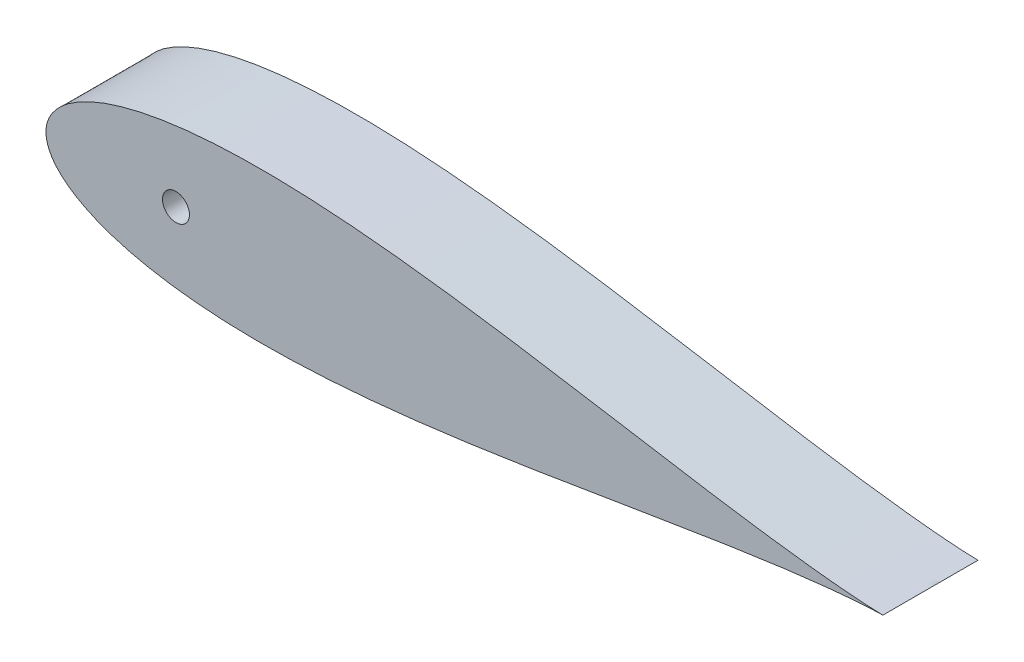
SolidWorks part; units mm, degrees
ref_plane "Front Plane" through (0, 0, 0) normal (0, 0, 1) x (1, 0, 0)
ref_plane "Top Plane" through (0, 0, 0) normal (0, 1, 0) x (1, 0, 0)
ref_plane "Right Plane" through (0, 0, 0) normal (1, 0, 0) x (0, 0, -1)
sketch "Sketch1" plane through (0, 0, 0) normal (0, 0, 1) x (1, 0, 0)
  line L0 (100, 0) -> (0, 0) construction
  line L1 (1.2169, -991.9959) -> (1.2169, 49008.0041) construction
  line L2 (93.345, 0) -> (114.935, 0) construction
  line L3 (125.634, 0) -> (131.6629, 0) construction
  line L4 (643.5991, 0) -> (643.5991, -1.016)
  line L9 (0, 0) -> (643.9668, 0)
  line L13 (460.661, 0) -> (473.361, 0)
  circle A0 centre (104.14, 0) radius 10.795 construction
  arc A1 (1.2169, -4.6585) -> (1.2169, 4.6585) centre (9.525, 0) cw
  arc A2 (641.5671, 0) -> (644.1071, 0) centre (642.8371, 0) ccw
  circle A4 centre (104.14, 0) radius 10.795
  circle A9 centre (40.64, 0) radius 12.7
  circle A14 centre (642.3793, 0) radius 1.5875 construction
  arc A15 (642.5108, -1.582) -> (642.5108, 1.582) centre (642.3793, 0) ccw
  spline S2 degree 3 poles (666.3448, -0.0547) (672.2538, 0) (666.3448, 0.0547) (662.8509, 0.2344) (656.505, 0.5436) (649.293, 1.0348) (640.4916, 1.7319) (630.4138, 2.6634) (619.0141, 3.8493) (606.375, 5.3044) (592.5439, 7.0376) (577.5855, 9.0506) (561.5643, 11.3389) (544.5497, 13.8907) (526.6141, 16.6877) (507.8326, 19.7051) (488.2827, 22.9117) (468.0444, 26.2704) (447.1994, 29.739) (425.8316, 33.2703) (404.0263, 36.8132) (381.8707, 40.3133) (359.4533, 43.7135) (336.8645, 46.9554) (314.1962, 49.9798) (291.5418, 52.7277) (268.9963, 55.1412) (246.6566, 57.1646) (224.6209, 58.7452) (202.9892, 59.8341) (181.8631, 60.3875) (161.3458, 60.367) (141.542, 59.7399) (122.5581, 58.4818) (104.5023, 56.5743) (87.485, 54.0089) (71.6197, 50.7848) (57.0237, 46.9125) (43.8205, 42.415) (32.1416, 37.3322) (22.1291, 31.7315) (13.9324, 25.7264) (7.6896, 19.5132) (3.4631, 13.4204) (1.1063, 7.9234) (0.1546, 3.5138) (-0.0622, 0) (0.1546, -3.5138) (1.1063, -7.9234) (3.4631, -13.4204) (7.6896, -19.5132) (13.9324, -25.7264) (22.1291, -31.7315) (32.1416, -37.3322) (43.8205, -42.415) (57.0237, -46.9125) (71.6197, -50.7848) (87.485, -54.0089) (104.5023, -56.5743) (122.5581, -58.4818) (141.542, -59.7399) (161.3458, -60.367) (181.8631, -60.3875) (202.9892, -59.8341) (224.6209, -58.7452) (246.6566, -57.1646) (268.9963, -55.1412) (291.5418, -52.7277) (314.1962, -49.9798) (336.8645, -46.9554) (359.4533, -43.7135) (381.8707, -40.3133) (404.0263, -36.8132) (425.8316, -33.2703) (447.1994, -29.739) (468.0444, -26.2704) (488.2827, -22.9117) (507.8326, -19.7051) (526.6141, -16.6877) (544.5497, -13.8907) (561.5643, -11.3389) (577.5855, -9.0506) (592.5439, -7.0376) (606.375, -5.3044) (619.0141, -3.8493) (630.4138, -2.6634) (640.4916, -1.7319) (649.293, -1.0348) (656.505, -0.5436) (662.8509, -0.2344) (666.3448, -0.0547) (672.2538, 0) (666.3448, 0.0547) knots -0.009667 -0.005395 -0.002168 0 0.002168 0.005395 0.009667 0.014967 0.021271 0.028553 0.036781 0.04592 0.055932 0.066773 0.078397 0.090755 0.103793 0.117456 0.131686 0.146422 0.1616 0.177156 0.193024 0.209135 0.225421 0.241812 0.258238 0.274629 0.290914 0.307025 0.322893 0.338448 0.353626 0.368361 0.38259 0.396253 0.40929 0.421647 0.43327 0.444109 0.454119 0.463255 0.471479 0.478755 0.485052 0.490344 0.49461 0.497833 0.5 0.502167 0.50539 0.509656 0.514948 0.521245 0.528521 0.536745 0.545881 0.555891 0.56673 0.578353 0.59071 0.603747 0.61741 0.631639 0.646374 0.661552 0.677107 0.692975 0.709086 0.725371 0.741762 0.758188 0.774579 0.790865 0.806976 0.822844 0.8384 0.853578 0.868314 0.882544 0.896207 0.909245 0.921603 0.933227 0.944068 0.95408 0.963219 0.971447 0.978729 0.985033 0.990333 0.994605 0.997832 1 1.002168 1.005395 1.009667 only from (670.56, 0) to (670.56, 0)
  point P2 (167.64, 0)
  point P8 (1.2169, -4.6585)
  point P10 (1.2169, 4.6585)
  point P28 (133.9182, 0)
  point P49 (130.0977, 0)
  point P59 (95.1064, 0)
  dimension "D2" = 21.59
  dimension "D3" = 1.016
  dimension "D4" = 1.27
  dimension "D8" = 25.4
  dimension "D9" = 63.5
  dimension "D10" = 3.175
  dimension "D6" = 63.5
extrude "Boss-Extrude1" add sketch "Sketch1" along normal blind 76.2 contours S2
sketch "Sketch3" plane through (0, 0, 76.2) normal (0, 0, 1) x (1, 0, 0)
  circle A0 centre (104.1392, 0) radius 10.795
  dimension "D1" = 21.59
extrude "Cut-Extrude2" cut sketch "Sketch3" against normal blind 76.2
sketch "Sketch4" plane through (0, 0, 76.2) normal (0, 0, 1) x (1, 0, 0)
sketch "Sketch6" plane through (0, 0, 0) normal (1, 0, 0) x (0, 0, -1)
  circle A0 centre (-20.32, 0) radius 6.35
  dimension "D1" = 12.7
  dimension "D2" = 20.32
extrude "Cut-Extrude3" cut sketch "Sketch6" against normal blind 0.0003 and the other way blind 53.34
sketch "Sketch7" plane through (0, 0, 0) normal (0, 0, -1) x (-1, 0, 0)
  circle A0 centre (-38.1, 0) radius 1.5875
  circle A1 centre (-50.8, 0) radius 1.5875
  point P4 (0, 0)
  dimension "D1" = 3.175
  dimension "D2" = 3.175
  dimension "D3" = 12.7
  dimension "D4" = 38.1
extrude "Cut-Extrude4" cut sketch "Sketch7" against normal blind 30.48
